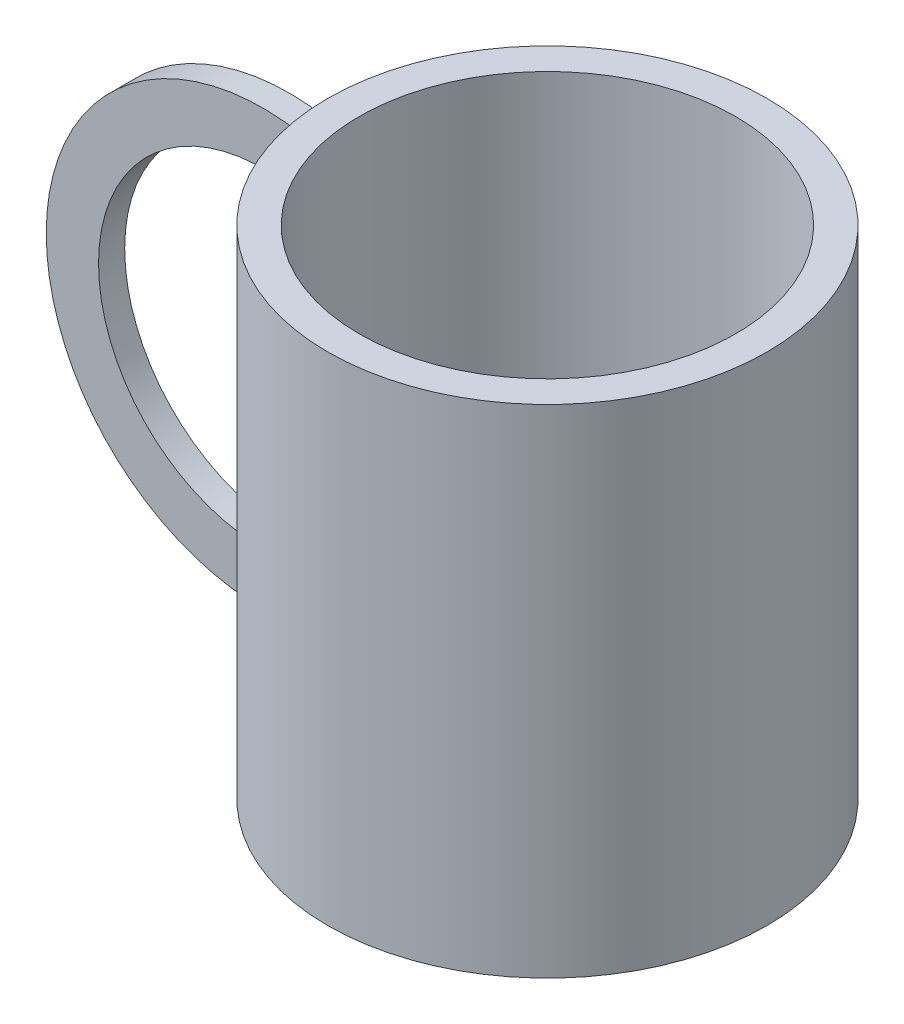
SolidWorks part; units mm, degrees
ref_plane "Alzado" through (0, 0, 0) normal (0, 0, 1) x (1, 0, 0)
ref_plane "Planta" through (0, 0, 0) normal (0, 1, 0) x (1, 0, 0)
ref_plane "Vista lateral" through (0, 0, 0) normal (1, 0, 0) x (0, 0, -1)
sketch "Croquis1" plane through (0, 0, 0) normal (0, 1, 0) x (1, 0, 0)
  circle A0 centre (0, 0) radius 36
  circle A1 centre (0, 0) radius 42
  dimension "D1" = 72
  dimension "D2" = 6
extrude "Saliente-Extruir1" add sketch "Croquis1" along normal blind 95
sketch "Croquis2" plane through (0, 0, 0) normal (0, -1, 0) x (1, 0, 0)
  circle A0 centre (0, 0) radius 42
extrude "Saliente-Extruir2" add sketch "Croquis2" against normal blind 5
sketch "Croquis3" plane through (0, 0, 0) normal (0, 0, 1) x (1, 0, 0)
  line L0 (-42, 95) -> (-42, 0) construction
  arc A0 (-42, 81.3333) -> (-42, 20.1199) centre (-49.3568, 50.7266) ccw
extrude "Extruir-Lámina1" add sketch "Croquis3" along normal blind 5 thin
